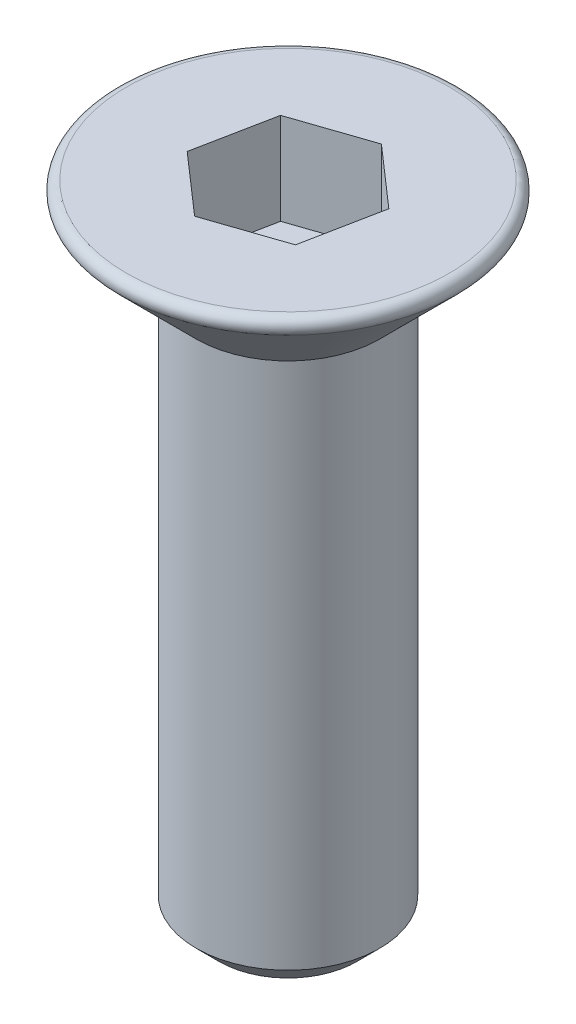
SolidWorks part; units mm, degrees
material "1.6523 (20NiCrMoS2-2)"
ref_plane "Front Plane" through (0, 0, 0) normal (0, 0, 1) x (1, 0, 0)
ref_plane "Top Plane" through (0, 0, 0) normal (0, 1, 0) x (1, 0, 0)
ref_plane "Right Plane" through (0, 0, 0) normal (1, 0, 0) x (0, 0, -1)
sketch "Sketch1" plane through (0, 0, 0) normal (0, 1, 0) x (1, 0, 0)
  circle A0 centre (0, 0) radius 2
  circle A1 centre (0, 0) radius 3.5
  dimension "D1" = 4
  dimension "D2" = 7
extrude "Boss-Extrude3" add sketch "Sketch1" against normal blind 12 contours A0
sketch "Sketch3" plane through (0, 0, 0) normal (0, 0, 1) x (1, 0, 0)
  line L4 (0, -2) -> (0, 2.3599) construction
  line L5 (-2, 0) -> (0, 0)
  line L6 (0, 2) -> (0, 0)
  line L7 (-2, 0) -> (-3.6586, 1.6586)
  line L8 (-3.5172, 2) -> (0, 2)
  arc A1 (-3.6586, 1.6586) -> (-3.5172, 2) centre (-3.5172, 1.8) cw
  point P4 (-4, 2)
  dimension "D3" = 0.2
  dimension "D1" = 8
  dimension "D2" = 45
revolve "Revolve2" add sketch "Sketch3" angle 360 about L4
chamfer "Chamfer2" distance 0.5 angle 45 1 edges at (0, -12, 2)
sketch "Sketch4" plane through (0, 2, 0) normal (0, 1, 0) x (1, 0, 0)
  line L1 (1.3031, -1.141) -> (1.6397, 0.558)
  line L2 (1.6397, 0.558) -> (0.3366, 1.699)
  line L3 (0.3366, 1.699) -> (-1.3031, 1.141)
  line L4 (-1.3031, 1.141) -> (-1.6397, -0.558)
  line L5 (-1.6397, -0.558) -> (-0.3366, -1.699)
  line L6 (-0.3366, -1.699) -> (1.3031, -1.141)
  circle A0 centre (0, 0) radius 1.5 construction
  dimension "D1" = 3
extrude "Cut-Extrude1" cut sketch "Sketch4" against normal blind 2
